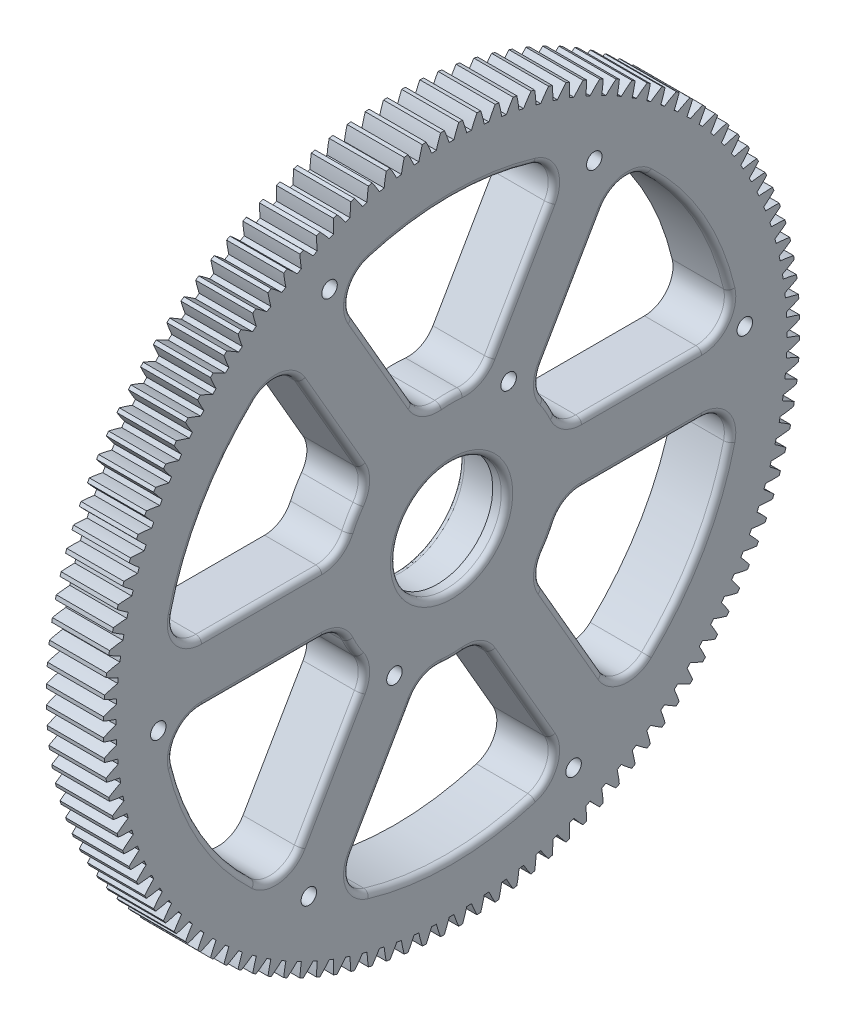
SolidWorks part; units mm, degrees
ref_plane "Plane1" through (0, 0, 0) normal (0, 0, 1) x (1, 0, 0)
ref_plane "Plane2" through (0, 0, 0) normal (0, 1, 0) x (1, 0, 0)
ref_plane "Plane3" through (0, 0, 0) normal (1, 0, 0) x (0, 0, -1)
other "Configuration Table"
sketch "HoldingSke" plane through (0, 0, 0) normal (0, 1, 0) x (1, 0, 0)
  line L0 (0, 0) -> (-254, -439.9409)
  line L1 (-15, 0) -> (100, 0) construction
  line L2 (0, 0) -> (-2.1039, 2.3779)
  line L3 (0, 0) -> (-11.863, 4.5341)
  line L4 (0, 0) -> (-4.318, 7.479)
  line L5 (0, 0) -> (-47.5972, -17.7524)
  line L6 (0, 0) -> (-10.5278, -7.1032)
  line L7 (-2.1039, 2.3779) -> (8.8308, 51.9871)
  line L8 (-76.2, 54.61) -> (-44.6786, 54.61)
  line L9 (-71.009, 38.7566) -> (-53.1078, 45.2721)
  line L10 (-76.2, 71.12) -> (104.1128, 71.12)
  line L11 (0, 0) -> (-12.7, 0)
  line L12 (-76.2, 101.6) -> (-76.1492, 101.6)
  line L13 (24.9733, 27.94) -> (52.9518, 28.4284)
  line L14 (24.9733, 27.94) -> (25.0241, 27.9398)
  line L15 (24.9733, 27.94) -> (100.4021, 29.52)
  circle A0 centre (0, 0) radius 14.2875
  circle A1 centre (0, 0) radius 38.1
  circle A2 centre (0, 0) radius 38.1
  circle A3 centre (0, 0) radius 14.2875
  dimension "MHD" = 76.2
  dimension "Hub_dia" = 76.2
  dimension "Bore" = 28.575
  dimension "MBD" = 28.575
  dimension "Num_teeth" = 120
  dimension "Pitch" = 508
  dimension "Overall_len" = 50.8
  dimension "Show_teeth" = 120
  dimension "Thickness" = 12.7
  dimension "OAL" = 50.8001
  dimension "T_dim" = 31.5214
  dimension "Ap" = 20
  dimension "H" = 19.05
  dimension "Pitch_radius" = 180.3128
  dimension "Width" = 12.7
  dimension "Backlash" = 0.0508
  dimension "Addendum_fac" = 1
  dimension "Dedendum_fac" = 1.2
  dimension "Clearance_fac" = 0.2
  dimension "Dedendum_add" = 0.0508
sketch "BasProSke" plane through (0, 0, 0) normal (0, 1, 0) x (1, 0, 0)
  line L0 (-10, 0) -> (60, 0) construction
  line L1 (0, 0) -> (0, 77.47)
  line L2 (0, 0) -> (12.7, 0)
  line L3 (12.7, 0) -> (12.7, 77.47)
  line L4 (12.7, 77.47) -> (0, 77.47)
  dimension "Thickness" = 12.7
  dimension "Diameter" = 154.94
revolve "Base-Revolve" add sketch "BasProSke" angle 360 about L0
sketch "TooCutSke" plane through (0, 0, 0) normal (1, 0, 0) x (0, 0, -1)
  line L1 (0, 0) -> (0, 107) construction
  line L2 (0, 0) -> (-1.0863, 76.1923) construction
  line L3 (0, 0) -> (-3.9891, 152.3369) construction
  line L4 (-1.0863, 76.1923) -> (-1.9945, 76.1685) construction
  arc A0 (0.5305, 74.6233) -> (-0.5305, 74.6233) centre (0, 0) ccw
  arc A1 (1.616, 77.4785) -> (-1.616, 77.4785) centre (0, 0) ccw
  circle A2 centre (0, 0) radius 76.2 construction
  circle A3 centre (0, 0) radius 71.6046 construction
  arc A4 (-0.5305, 74.6233) -> (-1.616, 77.4785) centre (-29.5279, 65.2328) ccw
  arc A5 (1.616, 77.4785) -> (0.5305, 74.6233) centre (29.5279, 65.2328) ccw
  dimension "Root_dia" = 149.2504
  dimension "Overcut_dia" = 154.9908
  dimension "Pitch_dia" = 152.4
  dimension "Base_dia" = 143.2092
  dimension "Flank_rad" = 30.48
  dimension "Half_ang" = 1.5
  dimension "Half_CT" = 0.9085
extrude "ToothCut" cut sketch "TooCutSke" along normal through all
fillet "Breaks" [suppressed] radius 0.0254
fillet "RootFillets" [suppressed] radius 0.3048
pattern_circular "TeethCuts" count 120 every 3 about axis through (-10, 0, 0) along (1, 0, 0) of "ToothCut", "RootFillets", "Breaks"
sketch "HubNeaOneSke" plane through (0, 0, 0) normal (-1, 0, 0) x (0, 0, 1)
  circle A0 centre (0, 0) radius 38.1
  dimension "Diameter" = 76.2
extrude "HubNearOne" [suppressed] add sketch "HubNeaOneSke" along normal blind 38.1001
sketch "HubNeaBotSke" plane through (0, 0, 0) normal (-1, 0, 0) x (0, 0, 1)
  circle A0 centre (0, 0) radius 38.1
  dimension "Diameter" = 76.2
extrude "HubNearBoth" [suppressed] add sketch "HubNeaBotSke" along normal blind 19.05
ref_plane "FarPln" through (12.7, 0, 0) normal (1, 0, 0) x (0, 0, -1)
sketch "HubFarSke" plane through (12.7, 0, 0) normal (1, 0, 0) x (0, 0, -1)
  circle A0 centre (0, 0) radius 38.1
  dimension "Diameter" = 76.2
extrude "HubFar" [suppressed] add sketch "HubFarSke" along normal blind 19.05
sketch "BorSke" plane through (0, 0, 0) normal (1, 0, 0) x (0, 0, -1)
  circle A0 centre (0, 0) radius 14.2875
  dimension "Diameter" = 28.575
extrude "Bore" cut sketch "BorSke" along normal mid plane 101.6001
sketch "KeySke" plane through (0, 0, 0) normal (1, 0, 0) x (0, 0, -1)
  line L0 (-3.175, 0) -> (-3.175, 17.2339)
  line L1 (-3.175, 17.2339) -> (3.175, 17.2339)
  line L2 (3.175, 17.2339) -> (3.175, 0)
  line L3 (0, 0) -> (0, 34) construction
  line L4 (-3.175, 0) -> (3.175, 0)
  dimension "Offset" = 17.2339
  dimension "Width" = 6.35
extrude "Keyway" [suppressed] cut sketch "KeySke" along normal mid plane 101.6001
pattern_circular "Keyway2" [suppressed] count 2 every 90 about axis through (-10, 0, 0) along (1, 0, 0)
sketch "Sketch2" plane through (12.7, 0, 0) normal (1, 0, 0) x (0, 0, -1)
  line L13 (8.5632, 28.4268) -> (21.9218, 51.5646)
  line L16 (-21.9218, 51.5646) -> (-8.5632, 28.4268)
  line L17 (0, 0) -> (0, 86.3173) construction
  arc A0 (2.4511, 25.2815) -> (-2.4511, 25.2815) centre (0, 0) ccw
  arc A1 (18.2473, 60.8218) -> (-18.2473, 60.8218) centre (0, 0) ccw
  arc A2 (21.9218, 51.5646) -> (18.2473, 60.8218) centre (16.4225, 54.7396) ccw
  arc A3 (2.4511, 25.2815) -> (8.5632, 28.4268) centre (3.0639, 31.6018) ccw
  arc A4 (-2.4511, 25.2815) -> (-8.5632, 28.4268) centre (-3.0639, 31.6018) cw
  arc A5 (-18.2473, 60.8218) -> (-21.9218, 51.5646) centre (-16.4225, 54.7396) ccw
  point P3 (0, 63.5)
  point P7 (0, 25.4)
  point P13 (6.35, 24.5934)
  point P16 (-6.35, 24.5934)
  dimension "D1" = 50.8
  dimension "D2" = 127
  dimension "D5" = 6.35
  dimension "D3" = 60
  dimension "D4" = 12.7
extrude "Cut-Extrude1" cut sketch "Sketch2" against normal up to surface (12.7 mm away) up to face at (0, 0, -14.2875)
pattern_circular "CirPattern1" count 6 over 360 about axis through (0, 0, 0) along (1, 0, 0) of "Cut-Extrude1"
sketch "Sketch3" plane through (12.7, 0, 0) normal (1, 0, 0) x (0, 0, -1)
  circle A0 centre (0, 0) radius 14.2875 construction
  circle A1 centre (0, 0) radius 14.2875
  circle A2 centre (0, 0) radius 12.3434 construction
  circle A3 centre (0, 0) radius 12.3434
extrude "Boss-Extrude2" add sketch "Sketch3" against normal up to surface (3.175 mm away)
fillet "Fillet1" radius 1.27 50 edges at (0, 0, -14.2875) (12.7, 57.0823, -22.3246) (12.7, 63.5, 0) (12.7, 57.0823, 22.3246) (12.7, 39.9957, 15.2425) (12.7, 25.9556, 5.9696) (12.7, 25.4, 0) (12.7, 25.9556, -5.9696) (12.7, 39.9957, -15.2425) (12.7, -57.0823, 22.3246) (12.7, -63.5, 0) (12.7, -57.0823, -22.3246) (12.7, -39.9957, -15.2425) (12.7, -25.9556, -5.9696) (12.7, -25.4, 0) (12.7, -25.9556, 5.9696) (12.7, -39.9957, 15.2425) (12.7, -9.2075, 60.597) (12.7, -31.75, 54.9926) (12.7, -47.8748, 38.2725) (12.7, -33.1982, 27.016) (12.7, -18.1476, 19.4934) (12.7, -12.7, 21.997) (12.7, -7.808, 25.463) (12.7, -6.7975, 42.2585) (12.7, -47.8748, -38.2725) (12.7, -31.75, -54.9926) (12.7, -9.2075, -60.597) (12.7, -6.7975, -42.2585) (12.7, -7.808, -25.463) (12.7, -12.7, -21.997) (12.7, -18.1476, -19.4934) (12.7, -33.1982, -27.016) (12.7, 9.2075, -60.597) (12.7, 31.75, -54.9926) (12.7, 47.8748, -38.2725) (12.7, 33.1982, -27.016) (12.7, 18.1476, -19.4934) (12.7, 12.7, -21.997) (12.7, 7.808, -25.463) (12.7, 6.7975, -42.2585) (12.7, 47.8748, 38.2725) (12.7, 31.75, 54.9926) (12.7, 9.2075, 60.597) (12.7, 6.7975, 42.2585) (12.7, 7.808, 25.463) (12.7, 12.7, 21.997) (12.7, 18.1476, 19.4934) (12.7, 33.1982, 27.016) (12.7, 0, -12.3434)
hole_wizard "#8-32 Tapped Hole1" positions "Sketch4" profile "Sketch5" tap size "#8-32" standard "ANSI Inch"
sketch "Sketch4" plane through (12.7, 0, 0) normal (1, 0, 0) x (0, 0, -1)
  point P0 (-27.1438, 59.6656)
  point P3 (12.7, 21.997)
  point P6 (31.75, 54.9926)
  point P9 (65.2438, 6.3256)
  point P12 (-12.7, -21.997)
  point P15 (-31.75, -54.9926)
  point P18 (-65.2438, -6.3256)
  point P21 (27.1438, -59.6656)
sketch "Sketch5" plane through (12.7, 59.6656, 27.1438) normal (0, 1, 0) x (0, 0, -1)
  line L0 (0, 0) -> (0, 13.7378)
  line L1 (0, 13.7378) -> (1.7272, 12.7)
  line L2 (1.7272, 12.7) -> (1.7272, 0)
  line L5 (1.7272, 0) -> (0, 0)
  line L10 (0, 13.7378) -> (-1.7272, 12.7) construction
  line L11 (0, -6.35) -> (0, 107.95) construction
  dimension "Tap Drill Dia." = 3.4544
  dimension "Tap Drill Depth" = 12.7
  dimension "Drill Angle" = 118
cosmetic thread "Hole Thread1" parameters "D1"=8.382, "D2"=4.1656
cosmetic thread "Hole Thread2" parameters "D1"=8.382, "D2"=4.1656
cosmetic thread "Hole Thread3" parameters "D1"=8.382, "D2"=4.1656
cosmetic thread "Hole Thread4" parameters "D1"=8.382, "D2"=4.1656
cosmetic thread "Hole Thread5" parameters "D1"=8.382, "D2"=4.1656
cosmetic thread "Hole Thread6" parameters "D1"=8.382, "D2"=4.1656
cosmetic thread "Hole Thread7" parameters "D1"=8.382, "D2"=4.1656
cosmetic thread "Hole Thread8" parameters "D1"=8.382, "D2"=4.1656
equation "' \"Pitch@HoldingSke\" = 4"
equation "' \"Num_teeth@HoldingSke\" = 12"
equation "' \"Ap@HoldingSke\" =  20"
equation "' \"Ap@HoldingSke\" = 20"
equation "' \"Width@HoldingSke\" = 0.5"
equation "' \"Hub_dia@HoldingSke\"= 1"
equation "' \"Hub_dia@HoldingSke\" = 1"
equation "' \"Overall_len@HoldingSke\" = 1.0"
equation "' \"Bore@HoldingSke\" = 0.75"
equation "' \"T_dim@HoldingSke\" = 0.85"
equation "' \"Width@KeySke\" = 0.25"
equation "' \"Show_teeth@HoldingSke\" = 13"
equation "' \"Backlash@HoldingSke\" = 0.009"
equation "' \"Addendum_fac@HoldingSke\" = 1.0"
equation "' \"Dedendum_fac@HoldingSke\" = 1.25"
equation "' \"Dedendum_add@HoldingSke\" = 0.00005"
equation "' \"Clearance_fac@HoldingSke\" = 0.25"
equation "' \"Pitch@HoldingSke\" = 0.5"
equation "' \"Num_teeth@HoldingSke\" = 23"
equation "' \"Show_teeth@HoldingSke\" = 23"
equation "' \"Backlash@HoldingSke\" = 0.0375"
equation "\"Overcut_dia@TooCutSke\" = (\"Num_teeth@HoldingSke\" + 2 * \"Addendum_fac@HoldingSke\") / \"Pitch@HoldingSke\" + 0.002"
equation "\"Pitch_dia@TooCutSke\" = \"Num_teeth@HoldingSke\" / \"Pitch@HoldingSke\""
equation "\"Base_dia@TooCutSke\" = \"Num_teeth@HoldingSke\" / \"Pitch@HoldingSke\" * cos((\"Ap@HoldingSke\"  * 3.14159265 / 180))"
equation "\"Root_dia@TooCutSke\" = (\"Num_teeth@HoldingSke\" + 2) / \"Pitch@HoldingSke\" - 2 * (\"Addendum_fac@HoldingSke\" + \"Dedendum_fac@HoldingSke\") / \"Pitch@HoldingSke\" - \"Dedendum_add@HoldingSke\" * 2"
equation "\"Half_ang@TooCutSke\" = 180 / \"Num_teeth@HoldingSke\""
equation "\"Half_CT@TooCutSke\" = \"Num_teeth@HoldingSke\" / \"Pitch@HoldingSke\" * sin((3.14159265 / 2 / \"Num_teeth@HoldingSke\")) / 2 - 7 * \"Backlash@HoldingSke\" / 4"
equation "\"Flank_rad@TooCutSke\" = \"Num_teeth@HoldingSke\" / \"Pitch@HoldingSke\" / 5"
equation "\"Radius@RootFillets\" = \"Clearance_fac@HoldingSke\" / \"Pitch@HoldingSke\" + \"Dedendum_add@HoldingSke\""
equation "\"Break_rad@Breaks\" = 0.02 / \"Pitch@HoldingSke\""
equation "\"Thickness@HoldingSke\" = \"Width@HoldingSke\""
equation "\"OAL@HoldingSke\" = \"Thickness@HoldingSke\""
equation "\"MHD@HoldingSke\" = (\"Num_teeth@HoldingSke\" + 2) / \"Pitch@HoldingSke\" - 2 * (\"Addendum_fac@HoldingSke\" + \"Dedendum_fac@HoldingSke\")  / \"Pitch@HoldingSke\" - \"Dedendum_add@HoldingSke\" * 2"
equation "\"MBD@HoldingSke\" = (\"Num_teeth@HoldingSke\" + 2) / \"Pitch@HoldingSke\" - 2 * (\"Addendum_fac@HoldingSke\" + \"Dedendum_fac@HoldingSke\")  / \"Pitch@HoldingSke\" - \"Dedendum_add@HoldingSke\" * 2 - 0.002"
equation "\"MHD@HoldingSke\" = ((sgn( \"MHD@HoldingSke\" - \"Hub_dia@HoldingSke\" )-1)*( \"MHD@HoldingSke\" - \"Hub_dia@HoldingSke\" ))/-2+ \"Hub_dia@HoldingSke\""
equation "\"MBD@HoldingSke\" = ((sgn( \"MBD@HoldingSke\" - \"Bore@HoldingSke\" )-1)*( \"MBD@HoldingSke\" - \"Bore@HoldingSke\" ))/-2+ \"Bore@HoldingSke\""
equation "\"OAL@HoldingSke\" = ((sgn( \"OAL@HoldingSke\" - \"Overall_len@HoldingSke\" )+1)*( \"OAL@HoldingSke\" - \"Overall_len@HoldingSke\" ))/2 + \"Overall_len@HoldingSke\" + 0.000002"
equation "\"Num_teeth@TeethCuts\" = int( \"Show_teeth@HoldingSke\" ) + 1"
equation "\"Num_teeth@TeethCuts\" = ((sgn( \"Num_teeth@TeethCuts\" - \"Num_teeth@HoldingSke\" )-1)*( \"Num_teeth@TeethCuts\" - \"Num_teeth@HoldingSke\" ))/-2+ \"Num_teeth@HoldingSke\""
equation "\"Num_teeth@TeethCuts\" = ((sgn( \"Num_teeth@TeethCuts\" - 2.0)+1)*( \"Num_teeth@TeethCuts\" - 2.0))/2 +2.0"
equation "\"Angle@TeethCuts\" = 360.0 / \"Num_teeth@HoldingSke\""
equation "\"Diameter@BasProSke\" = (\"Num_teeth@HoldingSke\" + 2 * \"Addendum_fac@HoldingSke\") / \"Pitch@HoldingSke\""
equation "\"Thickness@BasProSke\"  = \"Thickness@HoldingSke\""
equation "' \"Fillet_rad@BasProSke\" =  \"Thickness@HoldingSke\" * 0.05"
equation "' \"Fillet_rad@BasProSke\" = \"Thickness@HoldingSke\" * 0.05"
equation "\"MHD@HoldingSke\" = ((sgn( \"MHD@HoldingSke\" - \"Root_dia@TooCutSke\" )-1)*( \"MHD@HoldingSke\" - \"Root_dia@TooCutSke\" ))/-2+ \"Root_dia@TooCutSke\""
equation "\"Diameter@HubNeaOneSke\" = \"MHD@HoldingSke\""
equation "\"Length@HubNearOne\" = \"OAL@HoldingSke\" - \"Thickness@BasProSke\""
equation "\"Diameter@HubNeaBotSke\" = \"MHD@HoldingSke\""
equation "\"Length@HubNearBoth\" = ( \"OAL@HoldingSke\" - \"Thickness@BasProSke\" ) / 2.0"
equation "\"Thickness@FarPln\" = \"Thickness@BasProSke\""
equation "\"Diameter@HubFarSke\" = \"MHD@HoldingSke\""
equation "\"Length@HubFar\" = ( \"OAL@HoldingSke\" - \"Thickness@BasProSke\" ) / 2.0"
equation "\"Diameter@BorSke\" = \"MBD@HoldingSke\""
equation "\"D1@Bore\" = \"OAL@HoldingSke\" * 2.0"
equation "\"D1@Keyway\" = \"OAL@HoldingSke\" * 2.0"
equation "\"Offset@KeySke\" = \"T_dim@HoldingSke\" - \"MBD@HoldingSke\" / 2.0"
